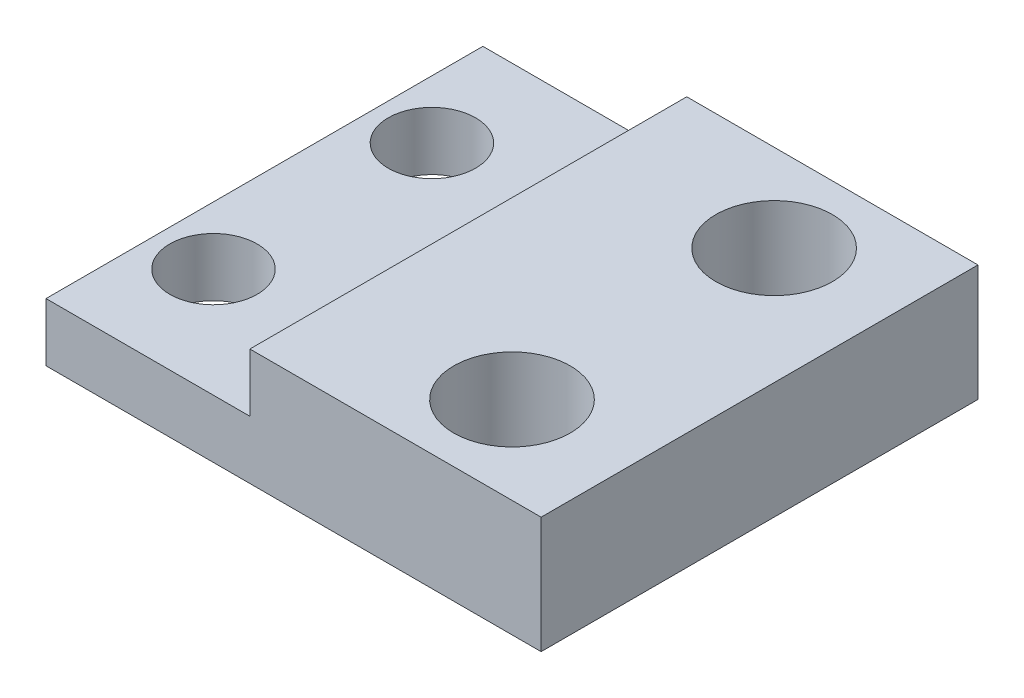
SolidWorks part; units mm, degrees
ref_plane "Alzado" through (0, 0, 0) normal (0, 0, 1) x (1, 0, 0)
ref_plane "Planta" through (0, 0, 0) normal (0, 1, 0) x (1, 0, 0)
ref_plane "Vista lateral" through (0, 0, 0) normal (1, 0, 0) x (0, 0, -1)
sketch "Croquis1" plane through (0, 0, 0) normal (0, 1, 0) x (1, 0, 0)
  line L1 (-10, 7.5) -> (10, 7.5)
  line L2 (-10, 7.5) -> (-10, -7.5)
  line L3 (-10, -7.5) -> (10, -7.5)
  line L4 (10, 7.5) -> (10, -7.5)
  line L5 (-10, 7.5) -> (10, -7.5) construction
  line L6 (-10, -7.5) -> (10, 7.5) construction
  circle A0 centre (-5, 3.75) radius 1.5
  circle A1 centre (-5, -3.75) radius 1.5
  circle A2 centre (6, 4.5) radius 2
  circle A3 centre (6, -4.5) radius 2
  point P0 (0, 0)
  dimension "D1" = 3
  dimension "D2" = 3
  dimension "D3" = 4
  dimension "D4" = 4
  dimension "D5" = 20
  dimension "D6" = 15
  dimension "D7" = 5
  dimension "D8" = 4
extrude "Saliente-Extruir1" add sketch "Croquis1" along normal blind 4
sketch "Croquis2" plane through (0, -3.5, 7.5) normal (0, 0, -1) x (1, 0, 0)
  line L5 (-10, -7.5) -> (0, -7.5)
  line L6 (-10, -7.5) -> (10, -7.5) construction
  line L7 (0, -7.5) -> (0, -5.5)
  line L8 (0, -5.5) -> (-7, -5.5)
  line L9 (-7, -5.5) -> (-7, -3.5)
  line L10 (-10, -3.5) -> (10, -3.5) construction
  line L11 (-7, -3.5) -> (-10, -3.5)
  line L13 (-10, -7.5) -> (-10, -3.5)
  dimension "D1" = 2
  dimension "D2" = 3
extrude "Cortar-Extruir1" cut sketch "Croquis2" along normal through all
